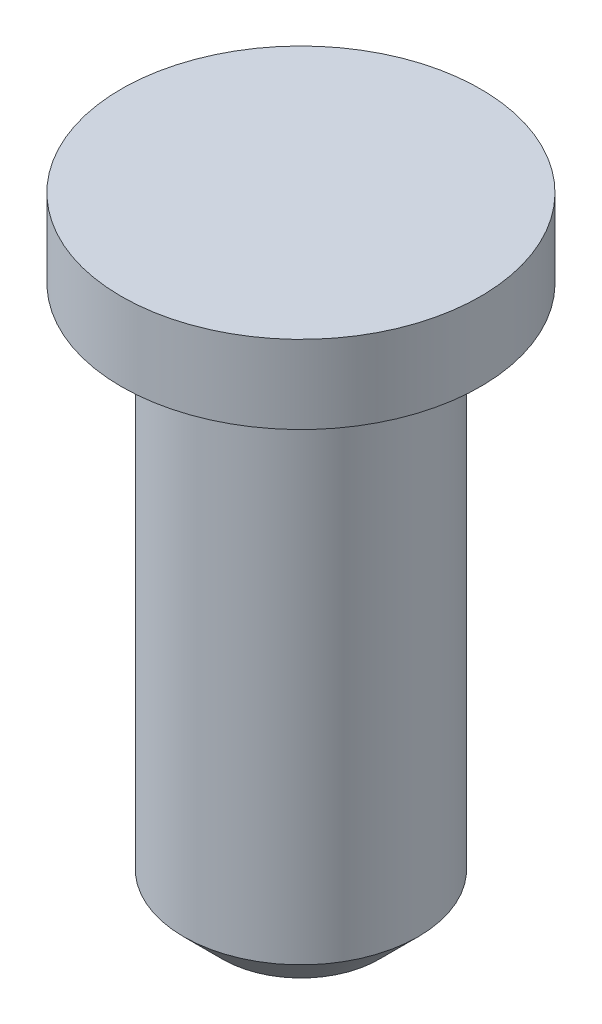
SolidWorks part; units mm, degrees
material "acero"
ref_plane "Alzado" through (0, 0, 0) normal (0, 0, 1) x (1, 0, 0)
ref_plane "Planta" through (0, 0, 0) normal (0, 1, 0) x (1, 0, 0)
ref_plane "Vista lateral" through (0, 0, 0) normal (1, 0, 0) x (0, 0, -1)
sketch "Croquis1" plane through (0, 0, 0) normal (0, 0, 1) x (1, 0, 0)
  line L0 (0, 0) -> (0, -60.9498) construction
  line L1 (0, 0) -> (2.3, 0)
  line L2 (2.3, 0) -> (2.3, -1)
  line L3 (2.3, -1) -> (1.5, -1)
  line L4 (1.5, -1) -> (1.5, -8)
  line L5 (1.5, -8) -> (0, -8)
  line L6 (0, -8) -> (0, 0)
  dimension "D1" = 8
  dimension "D2" = 1
  dimension "D3" = 4.6
  dimension "D4" = 3
revolve "Revolución1" add sketch "Croquis1" angle 360 about L0
chamfer "Chaflán1" distance 0.5 angle 45 1 edges at (0, -8, 1.5)
